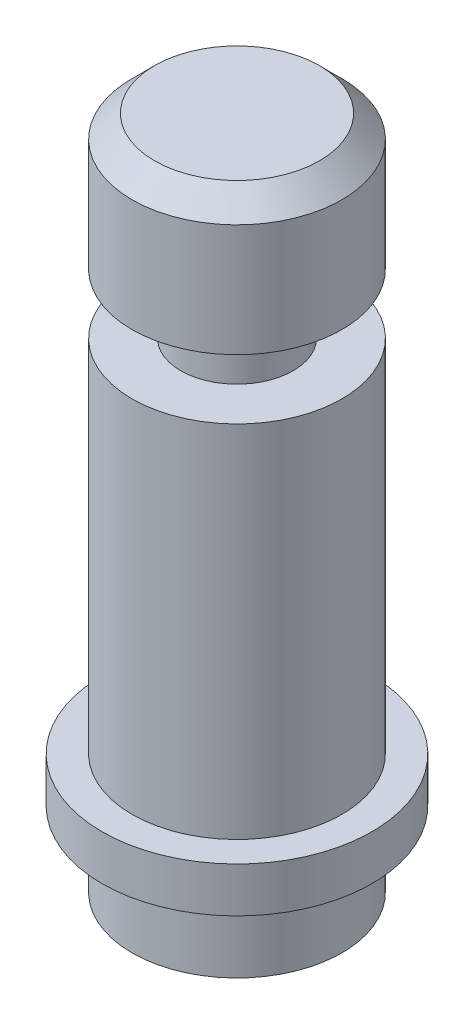
SolidWorks part; units mm, degrees
ref_plane "Alzado" through (0, 0, 0) normal (0, 0, 1) x (1, 0, 0)
ref_plane "Planta" through (0, 0, 0) normal (0, 1, 0) x (1, 0, 0)
ref_plane "Vista lateral" through (0, 0, 0) normal (1, 0, 0) x (0, 0, -1)
sketch "Croquis1" plane through (0, 0, 0) normal (0, 1, 0) x (1, 0, 0)
  circle A0 centre (0, 0) radius 9
  dimension "D1" = 18
extrude "Saliente-Extruir1" add sketch "Croquis1" along normal blind 3
sketch "Croquis2" plane through (0, 0, 0) normal (0, 1, 0) x (1, 0, 0)
  circle A0 centre (0, 0) radius 7
  dimension "D1" = 14
extrude "Saliente-Extruir2" add sketch "Croquis2" along normal blind 27
sketch "Croquis4" plane through (0, 27, 0) normal (0, 1, 0) x (1, 0, 0)
  circle A0 centre (0, 0) radius 3.75
  dimension "D1" = 7.5
extrude "Saliente-Extruir3" add sketch "Croquis4" along normal blind 4
sketch "Croquis5" plane through (0, 31, 0) normal (0, 1, 0) x (1, 0, 0)
  circle A0 centre (0, 0) radius 7
  circle A1 centre (0, 0) radius 7 construction
extrude "Saliente-Extruir4" add sketch "Croquis5" along normal blind 9
sketch "Croquis7" plane through (0, 0, 0) normal (0, -1, 0) x (1, 0, 0)
  circle A0 centre (0, 0) radius 7
  circle A1 centre (0, 0) radius 7 construction
extrude "Saliente-Extruir5" add sketch "Croquis7" along normal blind 5
chamfer "Chaflán1" distance 1.5 angle 45 1 edges at (0, 40, 7)
